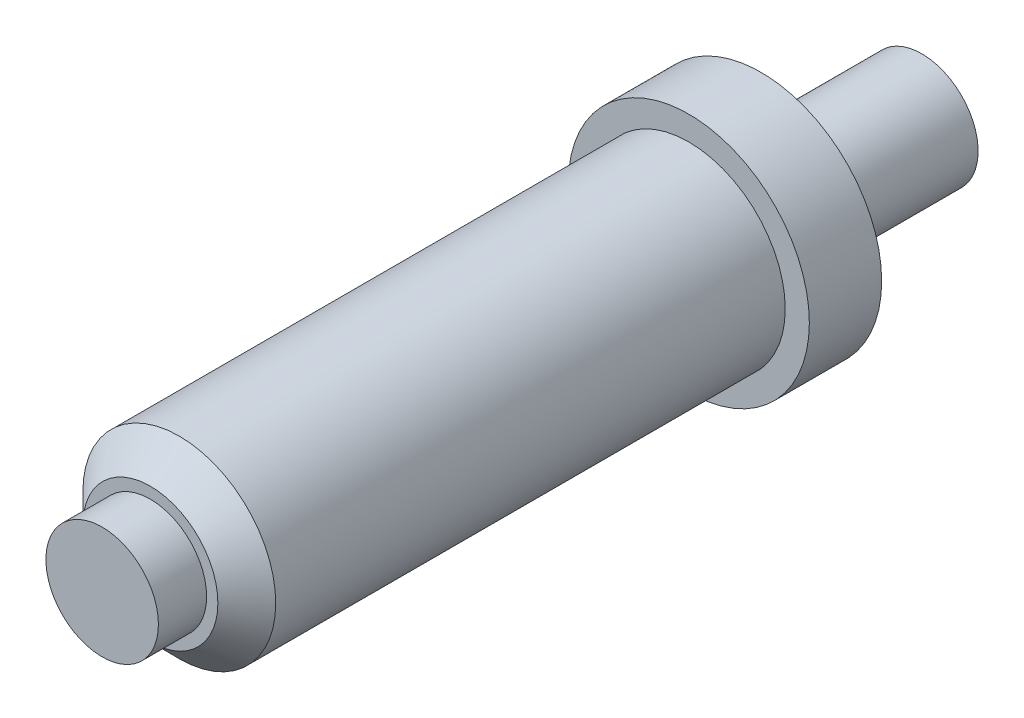
SolidWorks part; units mm, degrees
material "Сталь ШХ15 ГОСТ 801-78"
ref_plane "Plane1" through (0, 0, 0) normal (0, 0, 1) x (1, 0, 0)
ref_plane "Plane2" through (0, 0, 0) normal (0, 1, 0) x (1, 0, 0)
ref_plane "Plane3" through (0, 0, 0) normal (1, 0, 0) x (0, 0, -1)
sketch "Эскиз1" plane through (0, 0, 0) normal (0, 0, 1) x (1, 0, 0)
  circle A0 centre (0, 0) radius 6
  dimension "D1" = 12
extrude "Бобышка-Вытянуть1" add sketch "Эскиз1" along normal blind 38 contours A0
sketch "Эскиз2" plane through (0, 0, 38) normal (0, 0, 1) x (1, 0, 0)
  circle A0 centre (0, 0) radius 3.5
  dimension "D1" = 7
extrude "Бобышка-Вытянуть2" add sketch "Эскиз2" along normal blind 3 contours A0
sketch "Эскиз4" plane through (0, 0, 0) normal (0, 0, -1) x (-1, 0, 0)
  circle A0 centre (0, 0) radius 3.5
  dimension "D1" = 7
extrude "Бобышка-Вытянуть3" add sketch "Эскиз4" along normal blind 10
sketch "Эскиз6" plane through (0, 0, 0) normal (0, 0, -1) x (-1, 0, 0)
  circle A0 centre (0, 0) radius 7.5
  dimension "D1" = 15
extrude "Бобышка-Вытянуть5" add sketch "Эскиз6" against normal blind 4.5
chamfer "Фаска1" distance 1.8 angle 45 1 edges at (6, 0, 38)
